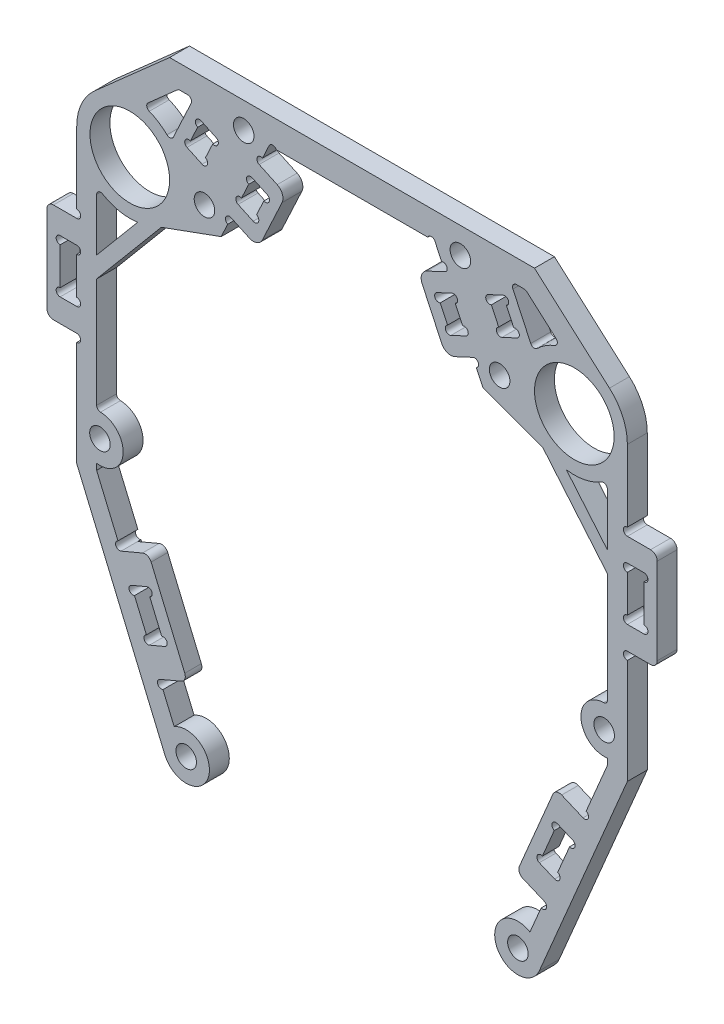
SolidWorks part; units mm, degrees
ref_plane "前视基准面" through (0, 0, 0) normal (0, 0, 1) x (1, 0, 0)
ref_plane "上视基准面" through (0, 0, 0) normal (0, 1, 0) x (1, 0, 0)
ref_plane "右视基准面" through (0, 0, 0) normal (1, 0, 0) x (0, 0, -1)
sketch "草图1" plane through (0, 0, 0) normal (0, 0, 1) x (1, 0, 0)
  line L0 (33.5, 0) -> (-33.5, 0) construction
  line L1 (-12.5, 12) -> (12.5, 12)
  line L2 (-12.5, 12) -> (-19.7282, -3.5009)
  line L3 (12.5, 12) -> (19.7282, -3.5009)
  line L4 (0, 12) -> (0, 0) construction
  line L5 (-30.7638, -7.5175) -> (-19.7282, -3.5009)
  line L6 (19.7282, -3.5009) -> (30.7638, -7.5175)
  line L7 (-38.804, 5.989) -> (-27.5, 16)
  line L8 (-27.5, 16) -> (27.5, 16)
  line L9 (27.5, 16) -> (38.804, 5.989)
  circle A0 centre (-33.5, 0) radius 6
  circle A1 centre (33.5, 0) radius 6
  arc A2 (-38.804, 5.989) -> (-30.7638, -7.5175) centre (-33.5, 0) ccw
  arc A3 (30.7638, -7.5175) -> (38.804, 5.989) centre (33.5, 0) ccw
  point P4 (0, 0)
  point P11 (0, 12)
  point P32 (0, 16)
  dimension "D1" = 67
  dimension "D2" = 12
  dimension "D3" = 2
  dimension "D4" = 25
  dimension "D5" = 12
  dimension "D6" = 50
  dimension "D7" = 4
  dimension "D8" = 140
  dimension "D9" = 55
extrude "凸台-拉伸1" add sketch "草图1" along normal mid plane 3
sketch "草图5" plane through (0, 0, 1.5) normal (0, 0, 1) x (1, 0, 0)
  line L0 (-14.001, 8.7811) -> (-9.9226, 6.8793)
  line L1 (-19.7282, -3.5009) -> (-12.5, 12) construction
  line L2 (-9.9226, 6.8793) -> (-14.1488, -2.1838)
  line L3 (-14.1488, -2.1838) -> (-18.2272, -0.282)
  line L4 (-18.2272, -0.282) -> (-14.001, 8.7811) construction
  line L5 (-14.001, 8.7811) -> (-15.0575, 6.5153)
  line L6 (-15.0575, 6.5153) -> (-12.7918, 5.4588)
  line L7 (-12.7918, 5.4588) -> (-14.9049, 0.9272)
  line L8 (-14.9049, 0.9272) -> (-17.1706, 1.9838)
  line L9 (-17.1706, 1.9838) -> (-18.2272, -0.282)
  line L10 (0, 12) -> (0, 0) construction
  line L11 (-12.5, 12) -> (12.5, 12) construction
  line L12 (14.9049, 0.9272) -> (17.1706, 1.9838)
  line L13 (12.7918, 5.4588) -> (14.9049, 0.9272)
  line L14 (15.0575, 6.5153) -> (12.7918, 5.4588)
  line L15 (14.001, 8.7811) -> (15.0575, 6.5153)
  line L16 (14.001, 8.7811) -> (9.9226, 6.8793)
  line L17 (9.9226, 6.8793) -> (14.1488, -2.1838)
  line L18 (14.1488, -2.1838) -> (18.2272, -0.282)
  line L19 (17.1706, 1.9838) -> (18.2272, -0.282)
  point P9 (-16.1141, 4.2496)
  dimension "D1" = 10
  dimension "D2" = 5
  dimension "D3" = 2.5
  dimension "D4" = 4.5
extrude "凸台-拉伸2" add sketch "草图5" against normal blind 3
sketch "草图6" plane through (0, 0, 1.5) normal (0, 0, 1) x (1, 0, 0)
  line L0 (-17.1706, 1.9838) -> (-15.0575, 6.5153) construction
  line L1 (-12.7918, 5.4588) -> (-14.9049, 0.9272) construction
  line L2 (-14.001, 8.7811) -> (-12.5, 12) construction
  line L3 (-19.7282, -3.5009) -> (-18.2272, -0.282) construction
  line L4 (0, 12) -> (0, 0) construction
  line L5 (-12.5, 12) -> (12.5, 12) construction
  line L6 (12.5, 12) -> (14.001, 8.7811) construction
  circle A0 centre (-15.3111, 5.9715) radius 0.6
  circle A1 centre (-13.0453, 4.915) radius 0.6
  circle A2 centre (-16.9171, 2.5276) radius 0.6
  circle A3 centre (-14.6513, 1.471) radius 0.6
  circle A4 centre (-13.7474, 9.3249) radius 0.6
  circle A5 centre (-18.4808, -0.8258) radius 0.6
  circle A6 centre (18.4808, -0.8258) radius 0.6
  circle A7 centre (13.7474, 9.3249) radius 0.6
  circle A8 centre (14.6513, 1.471) radius 0.6
  circle A9 centre (16.9171, 2.5276) radius 0.6
  circle A10 centre (13.0453, 4.915) radius 0.6
  circle A11 centre (15.3111, 5.9715) radius 0.6
  circle A12 centre (-11.9562, 11.7464) radius 0.6
  circle A13 centre (11.9562, 11.7464) radius 0.6
  dimension "D1" = 1.2
extrude "切除-拉伸2" cut sketch "草图6" against normal through all
fillet "圆角1" radius 1.5 4 edges at (9.9226, 6.8793, 0) (14.1488, -2.1838, 0) (-9.9226, 6.8793, 0) (-14.1488, -2.1838, 0)
sketch "草图7" plane through (0, 0, 1.5) normal (0, 0, 1) x (1, 0, 0)
  line L0 (-22.2445, -0.6154) -> (-16.3278, 12.0729) construction
  line L1 (-13.4939, 9.8687) -> (-12.5, 12) construction
  line L2 (-19.2862, 5.7287) -> (-13.8483, 3.193) construction
  line L3 (-13.2989, 4.3712) -> (-14.3977, 2.0148) construction
  line L4 (-19.7282, -3.5009) -> (-18.7343, -1.3696) construction
  line L5 (0, 12) -> (0, 0) construction
  line L6 (-11.4124, 12) -> (11.4124, 12) construction
  circle A0 centre (-22.2445, -0.6154) radius 1.55
  circle A1 centre (-16.3278, 12.0729) radius 1.55
  circle A2 centre (22.2445, -0.6154) radius 1.55
  circle A3 centre (16.3278, 12.0729) radius 1.55
  dimension "D1" = 3.1
  dimension "D2" = 14
  dimension "D3" = 3.5
extrude "切除-拉伸3" cut sketch "草图7" against normal through all
sketch "草图8" plane through (0, 0, 1.5) normal (0, 0, 1) x (1, 0, 0)
  line L0 (-26.173, 12.5) -> (-31.5318, 7.7541)
  line L1 (-21.1713, 0.5029) -> (-16.4947, 10.5319) construction
  line L2 (-27.5, 16) -> (-38.804, 5.989) construction
  line L8 (-14.9049, 0.9272) -> (-17.1706, 1.9838) construction
  line L9 (-16.6635, 3.0714) -> (-15.5647, 5.4278) construction
  line L10 (-26.173, 12.5) -> (-23.8523, 12.5)
  line L11 (27.5, 16) -> (-27.5, 16) construction
  line L12 (-16.1141, 4.2496) -> (-18.833, 5.5174) construction
  line L13 (0, 16) -> (0, 12) construction
  line L14 (-11.4124, 12) -> (11.4124, 12) construction
  line L27 (-13.2989, 4.3712) -> (-14.3977, 2.0148) construction
  line L28 (-15.0575, 6.5153) -> (-12.7918, 5.4588) construction
  line L29 (-14.9049, 0.9272) -> (-17.1706, 1.9838) construction
  line L30 (-13.2989, 4.3712) -> (-14.3977, 2.0148) construction
  line L31 (-15.0575, 6.5153) -> (-12.7918, 5.4588) construction
  line L32 (-16.6635, 3.0714) -> (-15.5647, 5.4278) construction
  line L33 (-22.1013, 5.6071) -> (-21.0025, 7.9635)
  line L34 (-20.4954, 9.051) -> (-22.7612, 10.1076)
  line L35 (-23.2683, 9.02) -> (-24.3671, 6.6636)
  line L36 (-24.8743, 5.576) -> (-22.6085, 4.5195)
  line L38 (24.8743, 5.576) -> (22.6085, 4.5195)
  line L40 (-27.3151, 5.0741) -> (-23.8523, 12.5)
  line L41 (23.2683, 9.02) -> (24.3671, 6.6636)
  line L42 (20.4954, 9.051) -> (22.7612, 10.1076)
  line L43 (22.1013, 5.6071) -> (21.0025, 7.9635)
  line L44 (26.173, 12.5) -> (23.8523, 12.5)
  line L45 (27.3151, 5.0741) -> (23.8523, 12.5)
  line L46 (26.173, 12.5) -> (31.5318, 7.7541)
  circle A1 centre (-33.5, 0) radius 6 construction
  arc A2 (-16.6635, 3.0714) -> (-17.1706, 1.9838) centre (-16.9171, 2.5276) ccw construction
  arc A4 (22.1013, 5.6071) -> (22.6085, 4.5195) centre (22.3549, 5.0633) ccw
  arc A6 (-14.9049, 0.9272) -> (-14.3977, 2.0148) centre (-14.6513, 1.471) ccw construction
  arc A7 (-13.2989, 4.3712) -> (-12.7918, 5.4588) centre (-13.0453, 4.915) ccw construction
  arc A8 (-15.0575, 6.5153) -> (-15.5647, 5.4278) centre (-15.3111, 5.9715) ccw construction
  arc A9 (-16.6635, 3.0714) -> (-17.1706, 1.9838) centre (-16.9171, 2.5276) ccw construction
  arc A10 (-14.9049, 0.9272) -> (-14.3977, 2.0148) centre (-14.6513, 1.471) ccw construction
  arc A11 (-13.2989, 4.3712) -> (-12.7918, 5.4588) centre (-13.0453, 4.915) ccw construction
  arc A12 (-15.0575, 6.5153) -> (-15.5647, 5.4278) centre (-15.3111, 5.9715) ccw construction
  arc A13 (-20.4954, 9.051) -> (-21.0025, 7.9635) centre (-20.749, 8.5072) cw
  arc A14 (-23.2683, 9.02) -> (-22.7612, 10.1076) centre (-23.0147, 9.5638) cw
  arc A15 (-24.8743, 5.576) -> (-24.3671, 6.6636) centre (-24.6207, 6.1198) cw
  arc A16 (-22.1013, 5.6071) -> (-22.6085, 4.5195) centre (-22.3549, 5.0633) cw
  arc A17 (24.8743, 5.576) -> (24.3671, 6.6636) centre (24.6207, 6.1198) ccw
  arc A18 (-27.3151, 5.0741) -> (-31.5318, 7.7541) centre (-33.5, 0) ccw
  circle A19 centre (-16.3278, 12.0729) radius 1.55 construction
  arc A20 (23.2683, 9.02) -> (22.7612, 10.1076) centre (23.0147, 9.5638) ccw
  arc A21 (20.4954, 9.051) -> (21.0025, 7.9635) centre (20.749, 8.5072) ccw
  arc A22 (27.3151, 5.0741) -> (31.5318, 7.7541) centre (33.5, 0) cw
  dimension "D1" = 3.5
  dimension "D2" = 2
  dimension "D4" = 0.5
  dimension "D3" = 2
  dimension "D5" = 3.5
extrude "切除-拉伸4" cut sketch "草图8" against normal through all
fillet "圆角2" radius 0.6 8 edges at (27.3151, 5.0741, 0) (23.8523, 12.5, 0) (31.5318, 7.7541, 0) (26.173, 12.5, 0) (-27.3151, 5.0741, 0) (-26.173, 12.5, 0) (-23.8523, 12.5, 0) (-31.5318, 7.7541, 0)
sketch "草图9" plane through (0, 0, 1.5) normal (0, 0, 1) x (1, 0, 0)
  line L0 (-41.5, 0) -> (-41.5, -39)
  line L1 (-38.5, -35.5359) -> (-38.5, -6.245)
  arc A0 (-38.804, 5.989) -> (-30.7638, -7.5175) centre (-33.5, 0) ccw construction
  arc A1 (-41.5, -39) -> (-38.5, -35.5359) centre (-38, -39) ccw
  arc A2 (-41.5, 0) -> (-38.5, -6.245) centre (-33.5, 0) ccw
  circle A3 centre (-38, -39) radius 1.55
  circle A4 centre (-33.5, 0) radius 6 construction
  point P9 (0, 0)
  point P12 (0, -19.5)
  dimension "D1" = 3
  dimension "D2" = 3.5
  dimension "D3" = 3.1
  dimension "D4" = 19.5
  dimension "D5" = 19.5
extrude "凸台-拉伸3" add sketch "草图9" against normal blind 3
mirror "镜向1" about plane through (0, 0, 0) normal (1, 0, 0) of "凸台-拉伸3"
fillet "圆角3" radius 0.6 4 edges at (38.5, -35.5359, 0) (38.5, -6.245, 0) (-38.5, -35.5359, 0) (-38.5, -6.245, 0)
sketch "草图10" plane through (0, 0, 1.5) normal (0, 0, 1) x (1, 0, 0)
  line L0 (-41.5, -12) -> (-46, -12)
  line L2 (-46, -12) -> (-46, -27)
  line L3 (-46, -27) -> (-41.5, -27)
  line L4 (-41.5, -27) -> (-41.5, -23.5)
  line L5 (-41.5, -23.5) -> (-44, -23.5)
  line L6 (-44, -23.5) -> (-44, -15.5)
  line L7 (-44, -15.5) -> (-41.5, -15.5)
  line L8 (-41.5, -15.5) -> (-41.5, -12)
  line L9 (0, 0) -> (0, 12) construction
  line L10 (-11.4124, 12) -> (11.4124, 12) construction
  line L11 (44, -15.5) -> (41.5, -15.5)
  line L12 (44, -23.5) -> (44, -15.5)
  line L13 (41.5, -23.5) -> (44, -23.5)
  line L14 (41.5, -27) -> (41.5, -23.5)
  line L15 (46, -27) -> (41.5, -27)
  line L16 (46, -12) -> (46, -27)
  line L17 (41.5, -12) -> (46, -12)
  line L18 (41.5, -15.5) -> (41.5, -12)
  line L19 (-41.5, 0) -> (-41.5, -39) construction
  circle A0 centre (-33.5, 0) radius 6 construction
  point P9 (-44, -19.5)
  dimension "D1" = 2.5
  dimension "D2" = 2
  dimension "D3" = 8
  dimension "D4" = 19.5
  dimension "D5" = 15
extrude "凸台-拉伸4" add sketch "草图10" against normal blind 3
sketch "草图11" plane through (0, 0, 1.5) normal (0, 0, 1) x (1, 0, 0)
  line L2 (-41.5, -27) -> (-41.5, -39) construction
  line L3 (-44, -15.5) -> (-44, -23.5) construction
  line L4 (0, 0) -> (0, 12) construction
  line L5 (-11.4124, 12) -> (11.4124, 12) construction
  line L6 (-41.5, 0) -> (-41.5, -12) construction
  line L7 (-41.5, -15.5) -> (-41.5, -23.5) construction
  circle A0 centre (-41.5, -11.4) radius 0.6
  circle A1 centre (-41.5, -27.6) radius 0.6
  circle A2 centre (-41.5, -22.9) radius 0.6
  circle A3 centre (-41.5, -16.1) radius 0.6
  circle A4 centre (-44, -16.1) radius 0.6
  circle A5 centre (-44, -22.9) radius 0.6
  circle A6 centre (44, -22.9) radius 0.6
  circle A7 centre (44, -16.1) radius 0.6
  circle A8 centre (41.5, -16.1) radius 0.6
  circle A9 centre (41.5, -22.9) radius 0.6
  circle A10 centre (41.5, -27.6) radius 0.6
  circle A11 centre (41.5, -11.4) radius 0.6
  point P2 (-41.5, -10.9132)
  point P4 (-41.5, -27.9067)
  point P12 (-41.5, -22.9)
  point P14 (-41.5, -22.1068)
  point P43 (-38.5, -11.1355)
  point P46 (0, 0)
  point P49 (-41.5, -17.0111)
  dimension "D1" = 1.2
extrude "切除-拉伸5" cut sketch "草图11" against normal through all
fillet "圆角4" radius 1 4 edges at (46, -27, 0) (46, -12, 0) (-46, -27, 0) (-46, -12, 0)
sketch "草图12" plane through (0, 0, 1.5) normal (0, 0, 1) x (1, 0, 0)
  line L0 (-38.5, -18.4046) -> (-27.3716, -5.1423)
  line L1 (-38.5, -34.9012) -> (-38.5, -7.3892) construction
  line L2 (-38.5, -15.2931) -> (-28.9037, -3.8567)
  line L3 (-38.5, -15.2931) -> (-38.5, -18.4046)
  line L4 (-28.9037, -3.8567) -> (-27.3716, -5.1423)
  line L5 (0, 0) -> (0, 16) construction
  line L6 (27.5, 16) -> (-27.5, 16) construction
  line L7 (38.5, -15.2931) -> (28.9037, -3.8567)
  line L8 (38.5, -15.2931) -> (38.5, -18.4046)
  line L9 (38.5, -18.4046) -> (27.3716, -5.1423)
  line L10 (28.9037, -3.8567) -> (27.3716, -5.1423)
  arc A0 (-37.593, -6.8737) -> (-30.7638, -7.5175) centre (-33.5, 0) ccw construction
  circle A1 centre (-33.5, 0) radius 6 construction
  dimension "D1" = 40
extrude "凸台-拉伸5" add sketch "草图12" against normal blind 3
sketch "草图13" plane through (0, 0, 1.5) normal (0, 0, 1) x (1, 0, 0)
  line L0 (-41.5, -39) -> (-41.5, -44)
  line L1 (-41.5, -28.2) -> (-41.5, -39) construction
  line L2 (-41.5, -44) -> (-28.2231, -75.3644)
  line L3 (-38.5, -42.4641) -> (-38.5, -43.3912)
  line L4 (-38.5, -43.3912) -> (-26.8108, -71.0049)
  line L5 (-38.5, -34.9012) -> (-38.5, -18.4046) construction
  line L6 (0, 16) -> (0, 0) construction
  line L7 (27.5, 16) -> (-27.5, 16) construction
  line L8 (41.5, -44) -> (28.2231, -75.3644)
  line L9 (41.5, -39) -> (41.5, -44)
  line L10 (38.5, -42.4641) -> (38.5, -43.3912)
  line L11 (38.5, -43.3912) -> (26.8108, -71.0049)
  arc A0 (-41.5, -39) -> (-37.9146, -35.501) centre (-38, -39) ccw construction
  circle A1 centre (-38, -39) radius 1.55 construction
  arc A2 (-41.5, -39) -> (-38.5, -42.4641) centre (-38, -39) ccw
  arc A3 (-28.2231, -75.3644) -> (-26.8108, -71.0049) centre (-25, -74) ccw
  circle A4 centre (-25, -74) radius 1.55
  arc A5 (41.5, -39) -> (38.5, -42.4641) centre (38, -39) cw
  arc A6 (28.2231, -75.3644) -> (26.8108, -71.0049) centre (25, -74) cw
  circle A7 centre (25, -74) radius 1.55
  point P17 (-41.5, -44.7554)
  dimension "D4" = 35
  dimension "D2" = 50
  dimension "D1" = 5
  dimension "D3" = 3
extrude "凸台-拉伸6" add sketch "草图13" against normal blind 3
sketch "草图17" plane through (0, 0, 1.5) normal (0, 0, 1) x (1, 0, 0)
  line L0 (-34.8162, -52.0936) -> (-30.6722, -50.3394)
  line L1 (-26.8108, -71.0049) -> (-38.5, -43.3912) construction
  line L2 (-30.6722, -50.3394) -> (-24.8248, -64.1527)
  line L3 (-24.8248, -64.1527) -> (-28.9688, -65.9069)
  line L4 (-28.9688, -65.9069) -> (-30.5281, -62.2233)
  line L5 (-30.5281, -62.2233) -> (-28.2259, -61.2488)
  line L6 (-28.2259, -61.2488) -> (-30.9547, -54.8026)
  line L7 (-30.9547, -54.8026) -> (-33.2569, -55.7771)
  line L8 (-33.2569, -55.7771) -> (-34.8162, -52.0936)
  line L9 (-29.5903, -58.0257) -> (-27.7485, -57.246) construction
  line L10 (0, 16) -> (0, 0) construction
  line L11 (27.5, 16) -> (-27.5, 16) construction
  line L12 (30.9547, -54.8026) -> (33.2569, -55.7771)
  line L13 (28.2259, -61.2488) -> (30.9547, -54.8026)
  line L14 (30.5281, -62.2233) -> (28.2259, -61.2488)
  line L15 (28.9688, -65.9069) -> (30.5281, -62.2233)
  line L16 (24.8248, -64.1527) -> (28.9688, -65.9069)
  line L17 (30.6722, -50.3394) -> (24.8248, -64.1527)
  line L18 (34.8162, -52.0936) -> (30.6722, -50.3394)
  line L19 (33.2569, -55.7771) -> (34.8162, -52.0936)
  arc A0 (-28.2231, -75.3644) -> (-26.8108, -71.0049) centre (-25, -74) ccw construction
  dimension "D1" = 7
  dimension "D2" = 2.5
  dimension "D3" = 2
  dimension "D4" = 15
  dimension "D5" = 16.5
extrude "凸台-拉伸9" add sketch "草图17" against normal blind 2.5
fillet "圆角8" radius 1 4 edges at (30.6722, -50.3394, 0.25) (24.8248, -64.1527, 0.25) (-30.6722, -50.3394, 0.25) (-24.8248, -64.1527, 0.25)
sketch "草图18" plane through (0, 0, 1.5) normal (0, 0, 1) x (1, 0, 0)
  line L0 (-30.5281, -62.2233) -> (-33.2569, -55.7771) construction
  line L1 (-30.9547, -54.8026) -> (-28.2259, -61.2488) construction
  line L2 (-26.8108, -71.0049) -> (-28.9688, -65.9069) construction
  line L3 (-34.8162, -52.0936) -> (-38.5, -43.3912) construction
  line L4 (0, 12) -> (0, 0) construction
  line L5 (-11.4124, 12) -> (11.4124, 12) construction
  circle A0 centre (-33.023, -56.3296) radius 0.6
  circle A1 centre (-30.7208, -55.3551) radius 0.6
  circle A2 centre (-30.762, -61.6708) radius 0.6
  circle A3 centre (-28.4598, -60.6963) radius 0.6
  circle A4 centre (-28.735, -66.4594) radius 0.6
  circle A5 centre (-35.0501, -51.541) radius 0.6
  circle A6 centre (35.0501, -51.541) radius 0.6
  circle A7 centre (28.735, -66.4594) radius 0.6
  circle A8 centre (28.4598, -60.6963) radius 0.6
  circle A9 centre (30.762, -61.6708) radius 0.6
  circle A10 centre (30.7208, -55.3551) radius 0.6
  circle A11 centre (33.023, -56.3296) radius 0.6
  dimension "D1" = 1.2
extrude "切除-拉伸7" cut sketch "草图18" against normal through all
